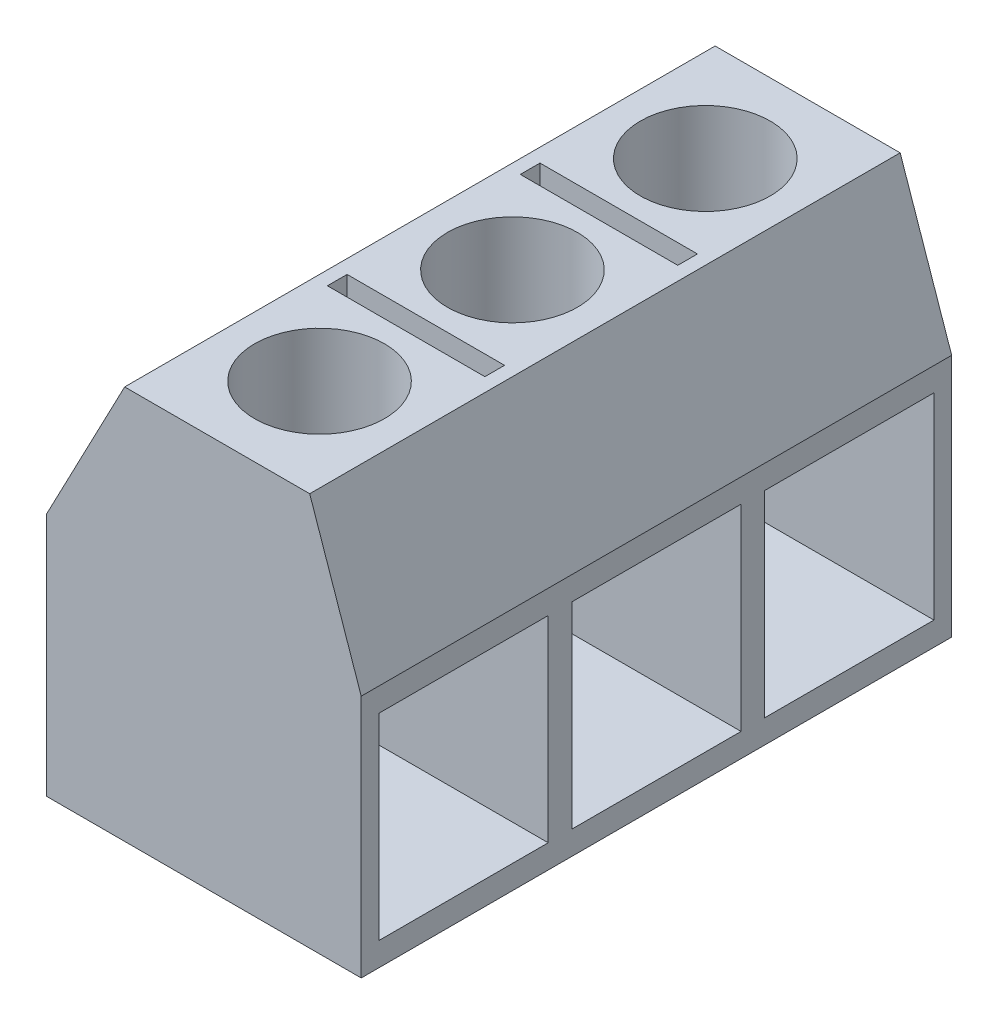
SolidWorks part; units mm, degrees
ref_plane "Front Plane" through (0, 0, 0) normal (0, 0, 1) x (1, 0, 0)
ref_plane "Top Plane" through (0, 0, 0) normal (0, 1, 0) x (1, 0, 0)
ref_plane "Right Plane" through (0, 0, 0) normal (1, 0, 0) x (0, 0, -1)
sketch "Sketch1" plane through (0, 0, 0) normal (0, 0, 1) x (1, 0, 0)
  line L0 (-3.8033, 0) -> (4.1967, 0)
  line L1 (4.1967, 0) -> (4.1967, 6.2)
  line L2 (4.1967, 6.2) -> (2.8877, 10)
  line L3 (2.8877, 10) -> (-1.8123, 10)
  line L4 (-1.8123, 10) -> (-3.8033, 6.2)
  line L5 (-3.8033, 6.2) -> (-3.8033, 0)
  dimension "D1" = 8
  dimension "D2" = 6.2
  dimension "D3" = 6.2
  dimension "D4" = 4.7
  dimension "D5" = 3.8
  dimension "D6" = 4.29
extrude "Boss-Extrude1" add sketch "Sketch1" along normal blind 15
sketch "Sketch2" plane through (0, 10, 0) normal (0, 1, 0) x (1, 0, 0)
  line L0 (2.8877, -15) -> (-1.8123, -15) construction
  line L1 (-1.4623, -10.2) -> (2.5377, -10.2)
  line L2 (-1.4623, -10.2) -> (-1.4623, -9.7)
  line L3 (-1.4623, -9.7) -> (2.5377, -9.7)
  line L4 (2.5377, -10.2) -> (2.5377, -9.7)
  line L5 (2.8877, -15) -> (2.8877, 0) construction
  line L6 (-1.8123, -9.7) -> (2.8877, -9.7) construction
  line L7 (-1.8123, -15) -> (-1.8123, 0) construction
  line L9 (-1.4623, -5.3) -> (2.5377, -5.3)
  line L10 (-1.4623, -5.3) -> (-1.4623, -4.8)
  line L11 (-1.4623, -4.8) -> (2.5377, -4.8)
  line L12 (2.5377, -5.3) -> (2.5377, -4.8)
  circle A0 centre (0.5377, -12.4) radius 1.65
  circle A1 centre (0.5377, -7.5) radius 1.65
  circle A2 centre (0.5377, -2.6) radius 1.65
  point P10 (0.5377, -10.2)
  dimension "D1" = 2.6
  dimension "D2" = 2.35
  dimension "D3" = 3.3
  dimension "D7" = 3.3
  dimension "D8" = 2.2
  dimension "D10" = 3.3
  dimension "D11" = 2.2
  dimension "D4" = 2.2
  dimension "D5" = 0.5
  dimension "D6" = 4
  dimension "D9" = 0.5
  dimension "D12" = 2.2
extrude "Cut-Extrude1" cut sketch "Sketch2" against normal blind 9.2
sketch "Sketch3" plane through (4.1967, 0, 0) normal (1, 0, 0) x (0, 0, -1)
  line L0 (-15, 0) -> (-15, 6.2) construction
  line L1 (-14.55, 5.6) -> (-10.25, 5.6)
  line L2 (-14.55, 5.6) -> (-14.55, 0.6)
  line L3 (-14.55, 0.6) -> (-10.25, 0.6)
  line L4 (-10.25, 5.6) -> (-10.25, 0.6)
  line L5 (-14.55, 5.6) -> (-10.25, 0.6) construction
  line L6 (-14.55, 0.6) -> (-10.25, 5.6) construction
  line L7 (-15, 6.2) -> (0, 6.2) construction
  line L8 (-9.65, 5.6) -> (-9.65, 0.6)
  line L9 (-9.65, 5.6) -> (-5.35, 5.6)
  line L10 (-5.35, 5.6) -> (-5.35, 0.6)
  line L11 (-9.65, 0.6) -> (-5.35, 0.6)
  line L12 (-4.75, 5.6) -> (-4.75, 0.6)
  line L13 (-4.75, 5.6) -> (-0.45, 5.6)
  line L14 (-0.45, 5.6) -> (-0.45, 0.6)
  line L15 (-4.75, 0.6) -> (-0.45, 0.6)
  point P0 (-12.4, 3.1)
  dimension "D1" = 4.3
  dimension "D2" = 0.45
  dimension "D3" = 5
  dimension "D4" = 0.6
  dimension "D5" = 0.6
  dimension "D6" = 0.6
extrude "Cut-Extrude2" cut sketch "Sketch3" against normal blind 6
